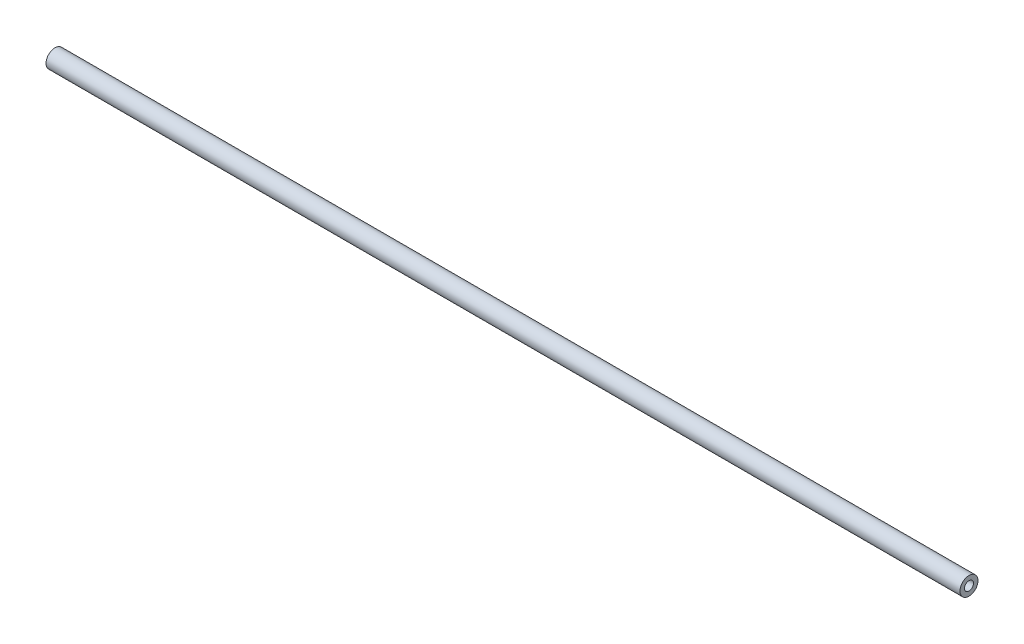
SolidWorks part; units mm, degrees
ref_plane "Alzado" through (0, 0, 0) normal (0, 0, 1) x (1, 0, 0)
ref_plane "Planta" through (0, 0, 0) normal (0, 1, 0) x (1, 0, 0)
ref_plane "Vista lateral" through (0, 0, 0) normal (1, 0, 0) x (0, 0, -1)
sketch "Croquis1" plane through (0, 0, 0) normal (1, 0, 0) x (0, 0, -1)
  circle A0 centre (0, 0) radius 4
  circle A1 centre (0, 0) radius 2
  dimension "D1" = 8
  dimension "D2" = 4
extrude "Saliente-Extruir1" add sketch "Croquis1" along normal mid plane 373
sketch "Croquis6" plane through (0, 0, 0) normal (0, 0, 1) x (1, 0, 0)
  line L0 (0, 0) -> (-130, 0) construction
  line L1 (0, 0) -> (130, 0) construction
  circle A0 centre (-130, 0) radius 2
  circle A1 centre (130, 0) radius 2
  dimension "D3" = 4
  dimension "D4" = 4
  dimension "D1" = 130
  dimension "D2" = 130
sketch "Sketch1" plane through (-186.5, 0, 0) normal (-1, 0, 0) x (0, 0, 1)
  circle A0 centre (0, 0) radius 4
  circle A1 centre (0, 0) radius 2
extrude "Boss-Extrude1" add sketch "Sketch1" along normal blind 32.85
